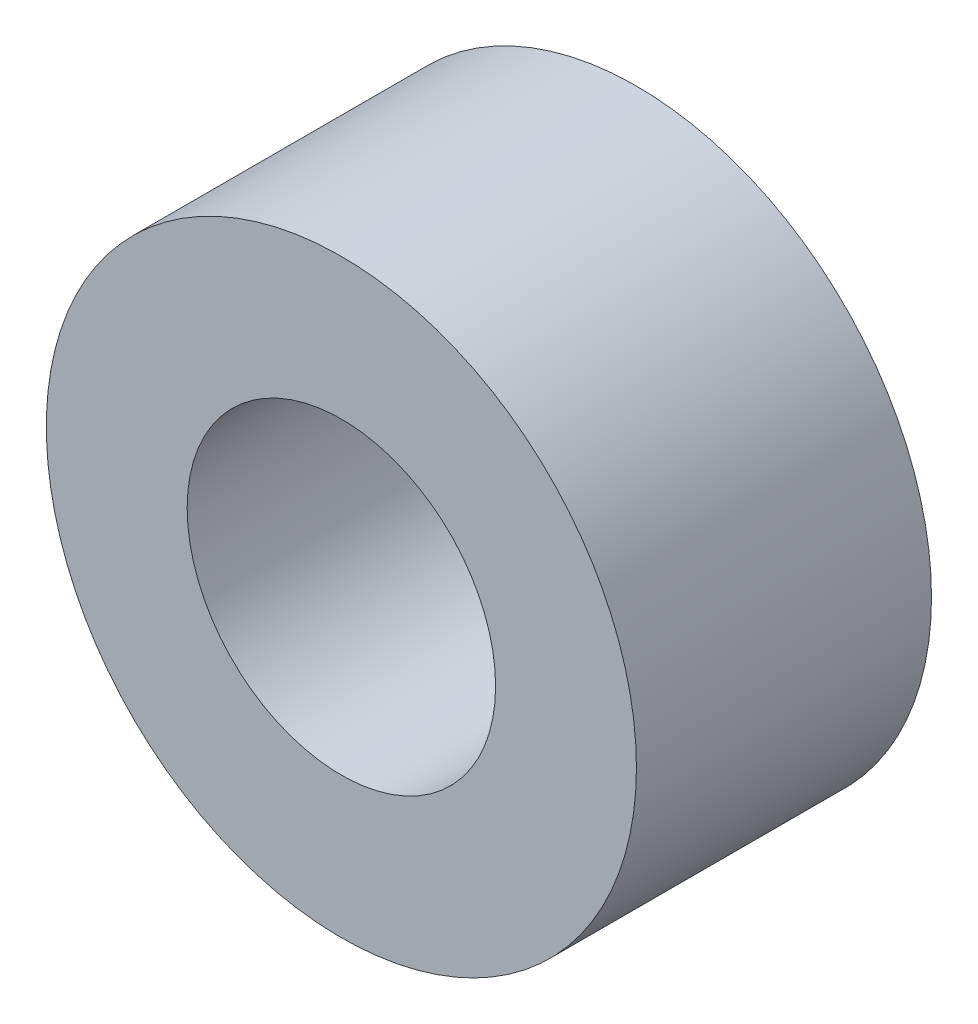
SolidWorks part; units mm, degrees
material "6061-T6 (SS)"
ref_plane "Front Plane" through (0, 0, 0) normal (0, 0, 1) x (1, 0, 0)
ref_plane "Top Plane" through (0, 0, 0) normal (0, 1, 0) x (1, 0, 0)
ref_plane "Right Plane" through (0, 0, 0) normal (1, 0, 0) x (0, 0, -1)
sketch "Sketch1" plane through (0, 0, 0) normal (0, 0, 1) x (1, 0, 0)
  circle A0 centre (0, 0) radius 4.7625
  circle A1 centre (0, 0) radius 2.4892
  dimension "D1" = 4.9784
  dimension "D2" = 9.525
extrude "Boss-Extrude1" add sketch "Sketch1" along normal blind 4.7625
